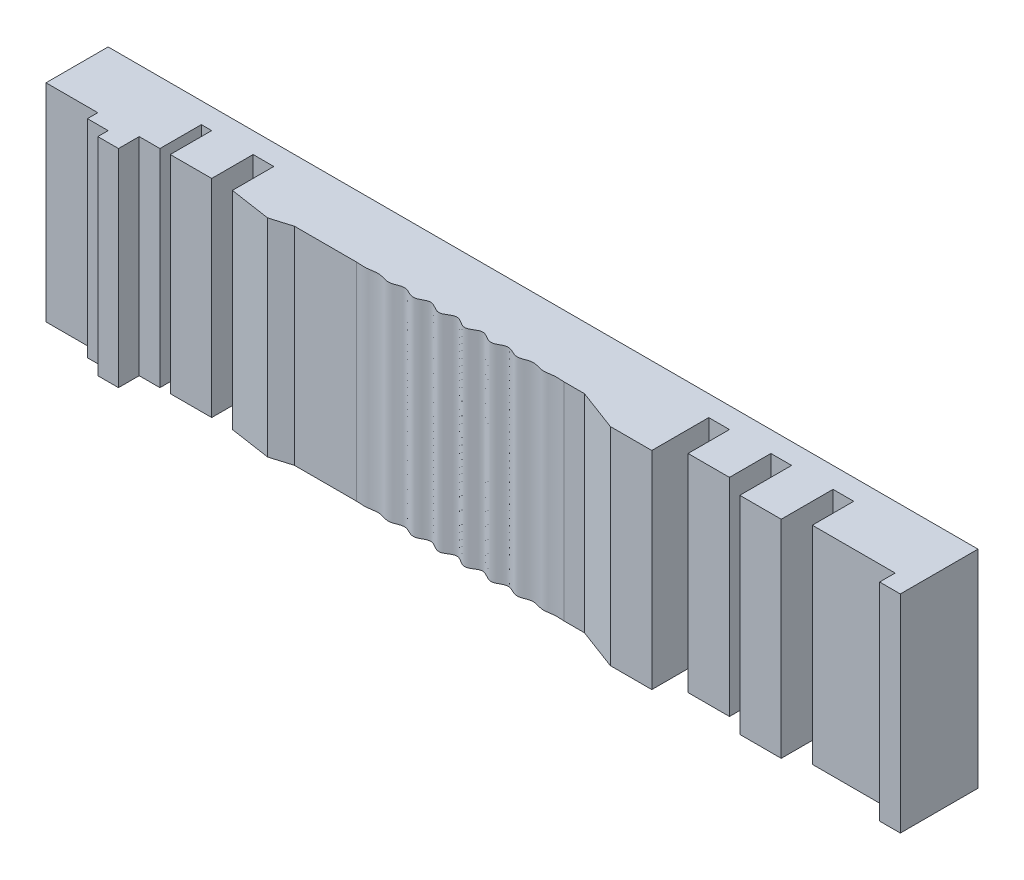
SolidWorks part; units mm, degrees
ref_plane "前视基准面" through (0, 0, 0) normal (0, 0, 1) x (1, 0, 0)
ref_plane "上视基准面" through (0, 0, 0) normal (0, 1, 0) x (1, 0, 0)
ref_plane "右视基准面" through (0, 0, 0) normal (1, 0, 0) x (0, 0, -1)
sketch "草图1" plane through (0, 0, 0) normal (0, 1, 0) x (1, 0, 0)
  line L0 (0, 0) -> (0, 3)
  line L1 (0, 3) -> (42, 3)
  line L2 (42, 3) -> (42, -0.75)
  line L3 (42, -0.75) -> (41, -0.75)
  line L4 (41, -0.75) -> (41, 0)
  line L5 (41, 0) -> (37, 0)
  line L6 (37, 0) -> (37, 2)
  line L7 (37, 2) -> (36, 2)
  line L8 (36, 2) -> (36, -0.5)
  line L9 (36, -0.5) -> (34, -0.5)
  line L10 (34, -0.5) -> (34, 2)
  line L11 (34, 2) -> (33, 2)
  line L12 (33, 2) -> (33, 0)
  line L13 (33, 0) -> (31, 0)
  line L14 (31, 0) -> (31, 2)
  line L15 (31, 2) -> (30, 2)
  line L16 (30, 2) -> (30, -0.75)
  line L17 (30, -0.75) -> (28, -0.75)
  line L18 (28, -0.75) -> (26, 0)
  line L19 (26, 0) -> (25, 0)
  line L20 (0, 0) -> (2.5, 0)
  line L21 (2.5, 0) -> (2.5, -0.5)
  line L22 (2.5, -0.5) -> (3.5, -0.5)
  line L23 (3.5, -0.5) -> (3.5, -1)
  line L24 (3.5, -1) -> (4.5, -1)
  line L25 (4.5, -1) -> (4.5, 0)
  line L26 (4.5, 0) -> (5.5, 0)
  line L27 (5.5, 0) -> (5.5, 2)
  line L28 (5.5, 2) -> (6, 2)
  line L29 (6, 2) -> (6, 0)
  line L30 (6, 0) -> (8, 0)
  line L31 (8, 0) -> (8, 2)
  line L32 (8, 2) -> (9, 2)
  line L33 (9, 2) -> (9, 0)
  line L34 (9, 0) -> (11, -0.3)
  line L35 (11, -0.3) -> (12, 0)
  line L36 (12, 0) -> (15, 0)
  spline S0 degree 4 poles (13.9999, 0.053) (14.0635, 0.0537) (14.1869, 0.0408) (14.3433, -0.0015) (14.5257, -0.0222) (14.6913, -0.0175) (14.7994, -0.0073) (14.9527, 0.0002) (15.0234, 0.0007) (15.171, -0.005) (15.3045, -0.017) (15.4743, -0.0215) (15.6887, 0.0049) (15.8939, 0.0519) (16.095, 0.0449) (16.2958, -0.0092) (16.4725, -0.0666) (16.6922, -0.0797) (16.8883, 0.0005) (17.0578, 0.0713) (17.22, 0.0944) (17.3473, 0.072) (17.4652, 0.0244) (17.5781, -0.0319) (17.6985, -0.0848) (17.8355, -0.1135) (17.9705, -0.0867) (18.0885, -0.0298) (18.1953, 0.0299) (18.2964, 0.0813) (18.4194, 0.121) (18.5654, 0.1118) (18.7072, 0.0391) (18.8498, -0.049) (19.0046, -0.1291) (19.1825, -0.1255) (19.3339, -0.041) (19.474, 0.0481) (19.6259, 0.1317) (19.8039, 0.1309) (19.9554, 0.0459) (20.0952, -0.0442) (20.2467, -0.13) (20.426, -0.1323) (20.5799, -0.0476) (20.7216, 0.0426) (20.8751, 0.1269) (21.0529, 0.1268) (21.2057, 0.0471) (21.3466, -0.0394) (21.4853, -0.1096) (21.6263, -0.1201) (21.7449, -0.0852) (21.8411, -0.0386) (21.9457, 0.0191) (22.0615, 0.0777) (22.2281, 0.1207) (22.3995, 0.0714) (22.5426, -0.0047) (22.6876, -0.0648) (22.8094, -0.0908) (22.9335, -0.0812) (23.0505, -0.0458) (23.1609, -0.002) (23.2703, 0.0379) (23.4073, 0.0699) (23.5987, 0.0655) (23.8208, -0.018) (24.0772, -0.0627) (24.3234, -0.0125) (24.5349, 0.0166) (24.7014, 0.0171) (24.8329, 0.0065) (24.9777, -0.0003) (25.0477, -0.001) (25.2013, 0.0049) (25.3082, 0.0165) (25.4426, 0.024) (25.5646, 0.0193) (25.6912, 0.0002) (25.813, -0.0277) (25.9061, -0.0462) (25.9686, -0.0531) (26, -0.0553) knots 0 0 0 0 0 0.020105 0.04021 0.050263 0.060315 0.070368 0.08042 0.087985 0.09555 0.11068 0.125809 0.140939 0.165176 0.177294 0.189412 0.207123 0.224834 0.245521 0.255864 0.266208 0.276283 0.286358 0.296432 0.306507 0.318374 0.330241 0.339312 0.348383 0.357453 0.366524 0.380144 0.393763 0.407383 0.421002 0.434517 0.448032 0.461547 0.475062 0.488608 0.502154 0.515699 0.529245 0.542955 0.556664 0.570373 0.584083 0.597491 0.6109 0.624308 0.637717 0.646276 0.654836 0.663396 0.671956 0.684299 0.696643 0.716675 0.726692 0.736708 0.74645 0.756191 0.765932 0.775674 0.784484 0.793294 0.810915 0.835555 0.860195 0.875022 0.889849 0.904676 0.912089 0.919503 0.929565 0.939627 0.949689 0.959751 0.969814 0.979876 0.989938 1 1 1 1 1 construction
  spline S1 degree 4 poles (15, 0) (15.0199, 0) (15.0602, -0.0007) (15.171, -0.005) (15.3045, -0.017) (15.4743, -0.0215) (15.6887, 0.0049) (15.8939, 0.0519) (16.095, 0.0449) (16.2958, -0.0092) (16.4725, -0.0666) (16.6922, -0.0797) (16.8883, 0.0005) (17.0578, 0.0713) (17.22, 0.0944) (17.3473, 0.072) (17.4652, 0.0244) (17.5781, -0.0319) (17.6985, -0.0848) (17.8355, -0.1135) (17.9705, -0.0867) (18.0885, -0.0298) (18.1953, 0.0299) (18.2964, 0.0813) (18.4194, 0.121) (18.5654, 0.1118) (18.7072, 0.0391) (18.8498, -0.049) (19.0046, -0.1291) (19.1825, -0.1255) (19.3339, -0.041) (19.474, 0.0481) (19.6259, 0.1317) (19.8039, 0.1309) (19.9554, 0.0459) (20.0952, -0.0442) (20.2467, -0.13) (20.426, -0.1323) (20.5799, -0.0476) (20.7216, 0.0426) (20.8751, 0.1269) (21.0529, 0.1268) (21.2057, 0.0471) (21.3466, -0.0394) (21.4853, -0.1096) (21.6263, -0.1201) (21.7449, -0.0852) (21.8411, -0.0386) (21.9457, 0.0191) (22.0615, 0.0777) (22.2281, 0.1207) (22.3995, 0.0714) (22.5426, -0.0047) (22.6876, -0.0648) (22.8094, -0.0908) (22.9335, -0.0812) (23.0505, -0.0458) (23.1609, -0.002) (23.2703, 0.0379) (23.4073, 0.0699) (23.5987, 0.0655) (23.8208, -0.018) (24.0772, -0.0627) (24.3234, -0.0125) (24.5349, 0.0166) (24.7014, 0.0171) (24.8329, 0.0065) (24.941, 0.0014) (24.9805, 0.0003) (25, 0) knots 0.08042 0.08042 0.08042 0.08042 0.08042 0.087985 0.09555 0.11068 0.125809 0.140939 0.165176 0.177294 0.189412 0.207123 0.224834 0.245521 0.255864 0.266208 0.276283 0.286358 0.296432 0.306507 0.318374 0.330241 0.339312 0.348383 0.357453 0.366524 0.380144 0.393763 0.407383 0.421002 0.434517 0.448032 0.461547 0.475062 0.488608 0.502154 0.515699 0.529245 0.542955 0.556664 0.570373 0.584083 0.597491 0.6109 0.624308 0.637717 0.646276 0.654836 0.663396 0.671956 0.684299 0.696643 0.716675 0.726692 0.736708 0.74645 0.756191 0.765932 0.775674 0.784484 0.793294 0.810915 0.835555 0.860195 0.875022 0.889849 0.904676 0.912089 0.919503 0.919503 0.919503 0.919503 0.919503
  dimension "D1" = 3
  dimension "D2" = 2.5
  dimension "D3" = 0.75
  dimension "D4" = 0.5
  dimension "D5" = 0.5
  dimension "D6" = 1
  dimension "D7" = 1
  dimension "D8" = 1
  dimension "D9" = 0.5
  dimension "D10" = 2
  dimension "D11" = 1
  dimension "D12" = 2
  dimension "D13" = 1
  dimension "D14" = 3
  dimension "D15" = 0.3
  dimension "D16" = 1
  dimension "D17" = 0.75
  dimension "D18" = 0.5
  dimension "D19" = 0
  dimension "D20" = 1
  dimension "D21" = 2
  dimension "D22" = 2
  dimension "D23" = 1
  dimension "D24" = 2
  dimension "D25" = 1
  dimension "D26" = 2
  dimension "D27" = 1
  dimension "D28" = 4
  dimension "D29" = 1
extrude "凸台-拉伸1" add sketch "草图1" along normal mid plane 10
